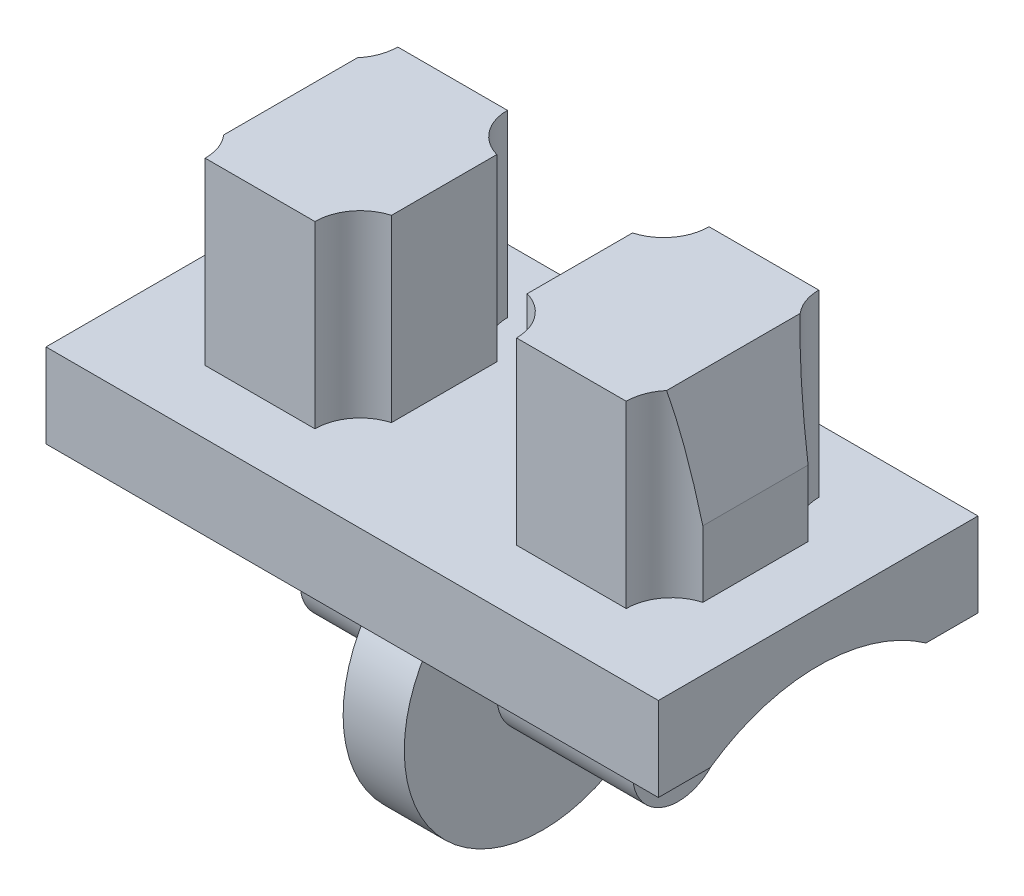
SolidWorks part; units mm, degrees
ref_plane "정면" through (0, 0, 0) normal (0, 0, 1) x (1, 0, 0)
ref_plane "평면" through (0, 0, 0) normal (0, 1, 0) x (1, 0, 0)
ref_plane "우측면" through (0, 0, 0) normal (1, 0, 0) x (0, 0, -1)
sketch "스케치1" plane through (0, 0, 0) normal (1, 0, 0) x (0, 0, -1)
  line L2 (-2.73, 2.7321) -> (-2.73, 2.1982)
  line L3 (2.73, 2.7321) -> (2.73, 2.1982)
  arc A1 (-2.73, 2.1982) -> (2.73, 2.1982) centre (0, 0) ccw
  arc A4 (2.73, 2.7321) -> (-2.73, 2.7321) centre (0, -1.155) ccw
  dimension "D1" = 3.505
  dimension "D2" = 4.75
  dimension "D3" = 2.73
  dimension "D4" = 2.7321
extrude "보스-돌출1" add sketch "스케치1" along normal mid plane 1.55
sketch "스케치2" plane through (0, 0, 0) normal (1, 0, 0) x (0, 0, -1)
  circle A0 centre (0, 0) radius 1.155
  dimension "D1" = 2.31
extrude "보스-돌출2" add sketch "스케치2" along normal mid plane 8.43
sketch "스케치3" plane through (0, 0, 0) normal (1, 0, 0) x (0, 0, -1)
  line L0 (-4.05, 2.73) -> (-2.73, 2.73)
  line L1 (-4.05, 4.86) -> (4.05, 4.86)
  line L2 (-4.05, 4.86) -> (-4.05, 2.73)
  line L4 (4.05, 2.73) -> (4.05, 4.86)
  line L5 (-2.73, 2.7321) -> (-2.73, 2.1982) construction
  line L6 (-2.73, 2.7321) -> (-2.73, 2.73)
  line L7 (2.73, 2.1982) -> (2.73, 2.7321) construction
  line L8 (2.73, 2.73) -> (2.73, 2.7321)
  line L9 (4.05, 2.73) -> (2.73, 2.73)
  arc A0 (2.73, 2.7321) -> (-2.73, 2.7321) centre (0, -1.155) ccw construction
  arc A1 (2.73, 2.7321) -> (-2.73, 2.7321) centre (0, -1.155) ccw
  dimension "D1" = 4.05
  dimension "D2" = 2.73
  dimension "D3" = 4.86
extrude "보스-돌출3" add sketch "스케치3" along normal mid plane 15.52
sketch "스케치4" plane through (0, 4.86, 0) normal (0, 1, 0) x (1, 0, 0)
  line L2 (-2.555, -2.44) -> (-5.335, -2.44)
  line L3 (-2.555, 2.44) -> (-5.335, 2.44)
  line L6 (-6.17, 1.334) -> (-6.17, -1.334)
  line L7 (-1.72, 1.334) -> (-1.72, -1.334)
  line L10 (-7.76, 4.05) -> (-7.76, -4.05) construction
  line L11 (7.76, -4.05) -> (-7.76, -4.05) construction
  arc A0 (-1.72, -1.334) -> (-2.555, -2.44) centre (-1.405, -2.44) ccw
  arc A1 (-2.555, 2.44) -> (-1.72, 1.334) centre (-1.405, 2.44) ccw
  arc A2 (-6.17, -1.334) -> (-5.335, -2.44) centre (-6.485, -2.44) cw
  arc A3 (-5.335, 2.44) -> (-6.17, 1.334) centre (-6.485, 2.44) cw
  dimension "D1" = 1.15
  dimension "D2" = 1.275
  dimension "D3" = 1.59
  dimension "D4" = 5.205
  dimension "D5" = 1.61
  dimension "D6" = 5.384
extrude "보스-돌출4" add sketch "스케치4" along normal blind 4.55
sketch "스케치5" plane through (0, 0, 0) normal (0, 0, 1) x (1, 0, 0)
  line L0 (-6.17, 6.54) -> (-5.6111, 9.41)
  line L1 (-5.335, 9.41) -> (-6.17, 9.41) construction
  line L3 (-6.17, 9.41) -> (-6.17, 4.86) construction
  line L4 (-5.6111, 9.41) -> (-6.17, 9.41)
  line L5 (-6.17, 9.41) -> (-6.17, 6.54)
  dimension "D1" = 11.02
  dimension "D2" = 1.68
extrude "컷-돌출1" cut sketch "스케치5" against normal mid plane 5
mirror "대칭 복사1" about plane through (0, 0, 0) normal (1, 0, 0) of "컷-돌출1", "보스-돌출4"
